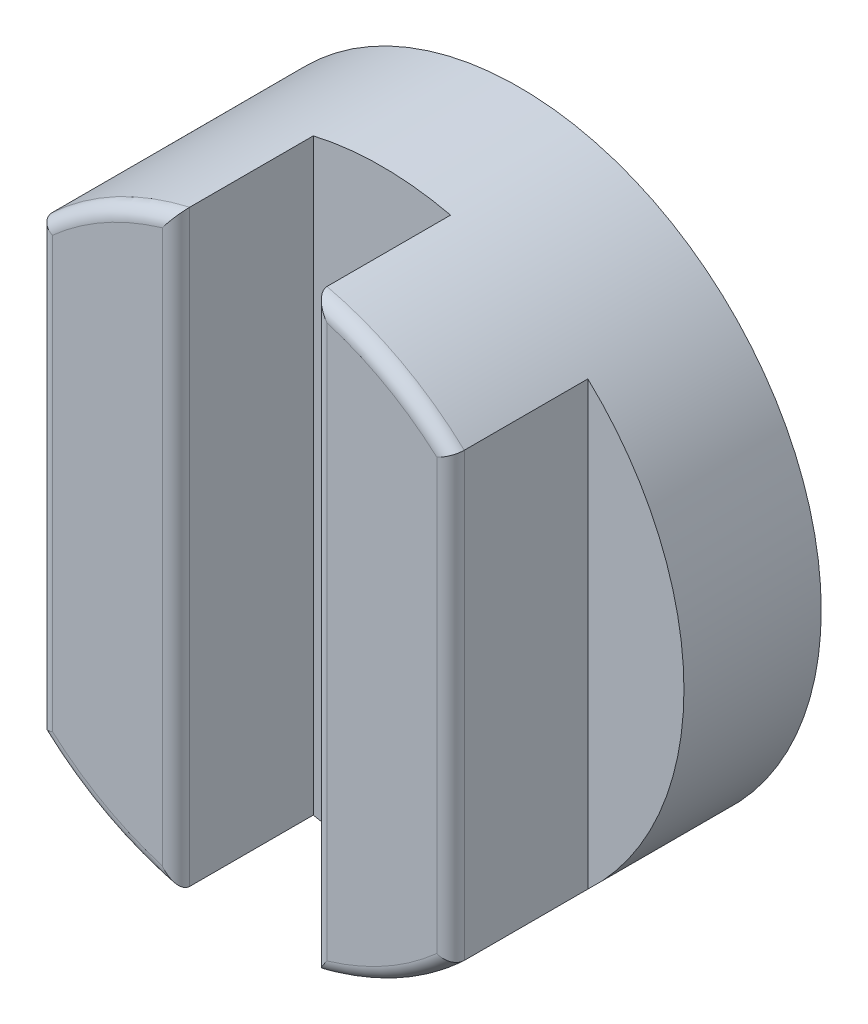
SolidWorks part; units mm, degrees
ref_plane "Plan de face" through (0, 0, 0) normal (0, 0, 1) x (1, 0, 0)
ref_plane "Plan de dessus" through (0, 0, 0) normal (0, 1, 0) x (1, 0, 0)
ref_plane "Plan de droite" through (0, 0, 0) normal (1, 0, 0) x (0, 0, -1)
sketch "Esquisse1" plane through (0, 0, 0) normal (0, 0, 1) x (1, 0, 0)
  circle A0 centre (0, 0) radius 11
  dimension "D1" = 22
extrude "Boss.-Extru.1" add sketch "Esquisse1" along normal blind 5
sketch "Esquisse2" plane through (0, 0, 5) normal (0, 0, 1) x (1, 0, 0)
  line L0 (0, 5.7045) -> (0, -6.8994) construction
  line L1 (-7.5, 8.0467) -> (-7.5, -8.0467)
  line L2 (-2.5, 10.7121) -> (-2.5, -10.7121)
  line L3 (7.5, 8.0467) -> (7.5, -8.0467)
  line L4 (2.5, 10.7121) -> (2.5, -10.7121)
  circle A0 centre (0, 0) radius 11 construction
  arc A1 (-2.5, -10.7121) -> (2.5, -10.7121) centre (0, 0) ccw
  arc A2 (2.5, 10.7121) -> (-2.5, 10.7121) centre (0, 0) ccw
  circle A3 centre (0, 0) radius 11
  circle M1 centre (0, 0) radius 11
  dimension "D1" = 5
  dimension "D2" = 5
extrude "Boss.-Extru.3" add sketch "Esquisse2" along normal blind 5 contours L2 L1 M1 | L4 L3 M1
fillet "Congé3" radius 0.5 8 edges at (5.1746, 9.7069, 10) (5.1746, -9.7069, 10) (7.5, 0, 10) (2.5, 0, 10) (-5.1746, 9.7069, 10) (-5.1746, -9.7069, 10) (-2.5, 0, 10) (-7.5, 0, 10)
